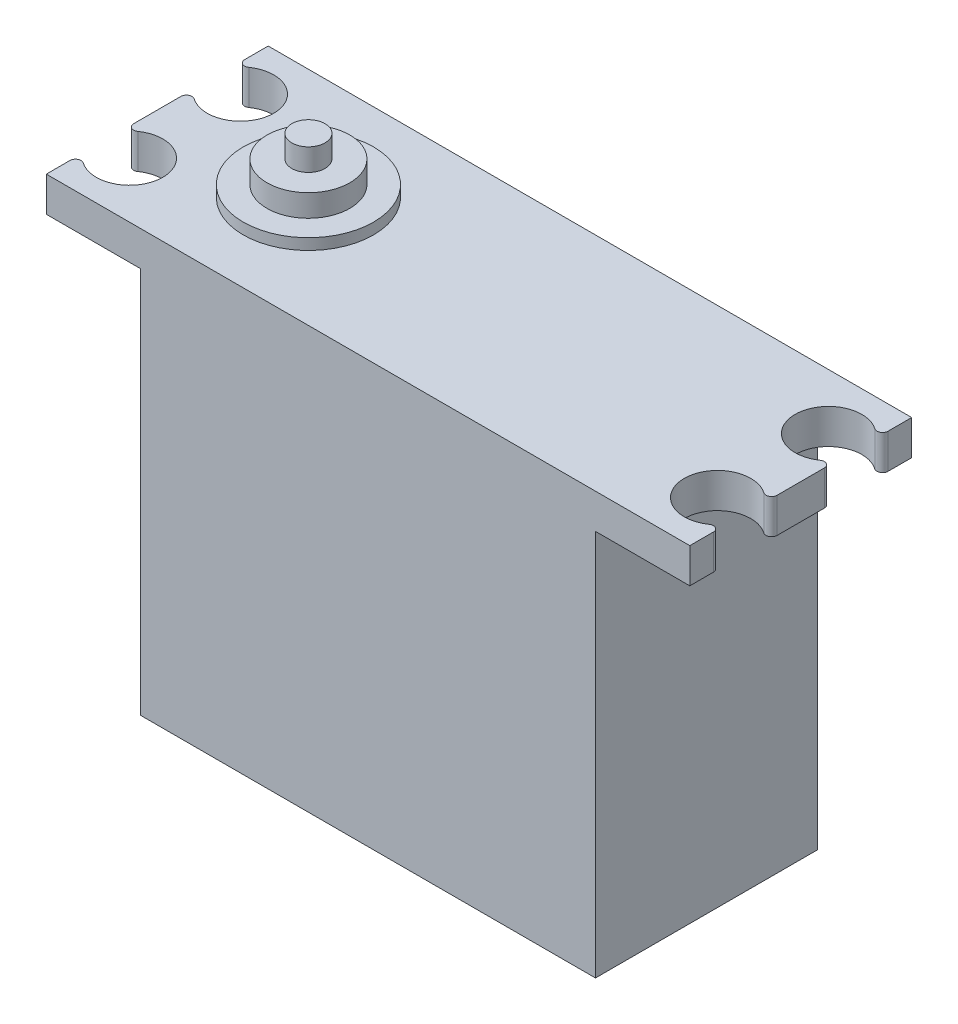
SolidWorks part; units mm, degrees
ref_plane "Front Plane" through (0, 0, 0) normal (0, 0, 1) x (1, 0, 0)
ref_plane "Top Plane" through (0, 0, 0) normal (0, 1, 0) x (1, 0, 0)
ref_plane "Right Plane" through (0, 0, 0) normal (1, 0, 0) x (0, 0, -1)
sketch "Sketch1" plane through (0, 0, 0) normal (0, 0, 1) x (1, 0, 0)
  line L0 (-29, 19) -> (29, 19)
  line L1 (20.5, -19) -> (-20.5, -19)
  line L2 (20.5, -19) -> (20.5, 15.8627)
  line L3 (20.5, 17) -> (-20.5, 17)
  line L4 (-20.5, -19) -> (-20.5, 15.8627)
  line L7 (-20.5, 15.8627) -> (-29, 15.8627)
  line L8 (29, 19) -> (29, 15.8627)
  line L9 (29, 15.8627) -> (20.5, 15.8627)
  line L10 (-29, 19) -> (-29, 15.8627)
  point P0 (0, 0)
  point P6 (0, 17)
  dimension "D1" = 41
  dimension "D2" = 36
extrude "Boss-Extrude1" add sketch "Sketch1" against normal blind 20 contours L0 L8 L9 L2 L1 L4 L7 L10
sketch "Sketch2" plane through (0, 19, 0) normal (0, 1, 0) x (1, 0, 0)
  line L0 (-29, 10) -> (31.146, 10) construction
  line L1 (-29, 20) -> (-29, 0) construction
  line L2 (0, 0) -> (0, 20) construction
  line L3 (-29, 0) -> (29, 0) construction
  line L4 (-29, 20) -> (29, 20) construction
  line L5 (29, 20) -> (29, 0) construction
  circle A0 centre (26.5, 5) radius 3
  circle A1 centre (26.5, 15) radius 3
  circle A2 centre (-26.5, 5) radius 3
  circle A3 centre (-26.5, 15) radius 3
  dimension "D1" = 6
  dimension "D2" = 2.5
  dimension "D3" = 10
extrude "Cut-Extrude2" cut sketch "Sketch2" against normal through all
fillet "Fillet1" radius 0.5 8 edges at (-29, 17.4314, -13.3417) (-29, 17.4314, -16.6583) (-29, 17.4314, -3.3417) (-29, 17.4314, -6.6583) (29, 17.4314, -16.6583) (29, 17.4314, -13.3417) (29, 17.4314, -6.6583) (29, 17.4314, -3.3417)
sketch "Sketch4" plane through (0, 19, 0) normal (0, 1, 0) x (1, 0, 0)
  line L0 (-29, 10) -> (29, 10) construction
  line L1 (-29, 12.1277) -> (-29, 7.8723) construction
  line L2 (29, 12.1277) -> (29, 7.8723) construction
  circle A0 centre (-15.3758, 10) radius 5.8721
extrude "Boss-Extrude2" add sketch "Sketch4" along normal blind 1
sketch "Sketch5" plane through (0, 20, 0) normal (0, 1, 0) x (1, 0, 0)
  circle A0 centre (-15.3758, 10) radius 3.7328
extrude "Boss-Extrude3" add sketch "Sketch5" along normal blind 2
sketch "Sketch8" plane through (0, 22, 0) normal (0, 1, 0) x (1, 0, 0)
  circle A0 centre (-15.3758, 10) radius 1.5
  dimension "D1" = 3
extrude "Boss-Extrude4" add sketch "Sketch8" along normal blind 2
